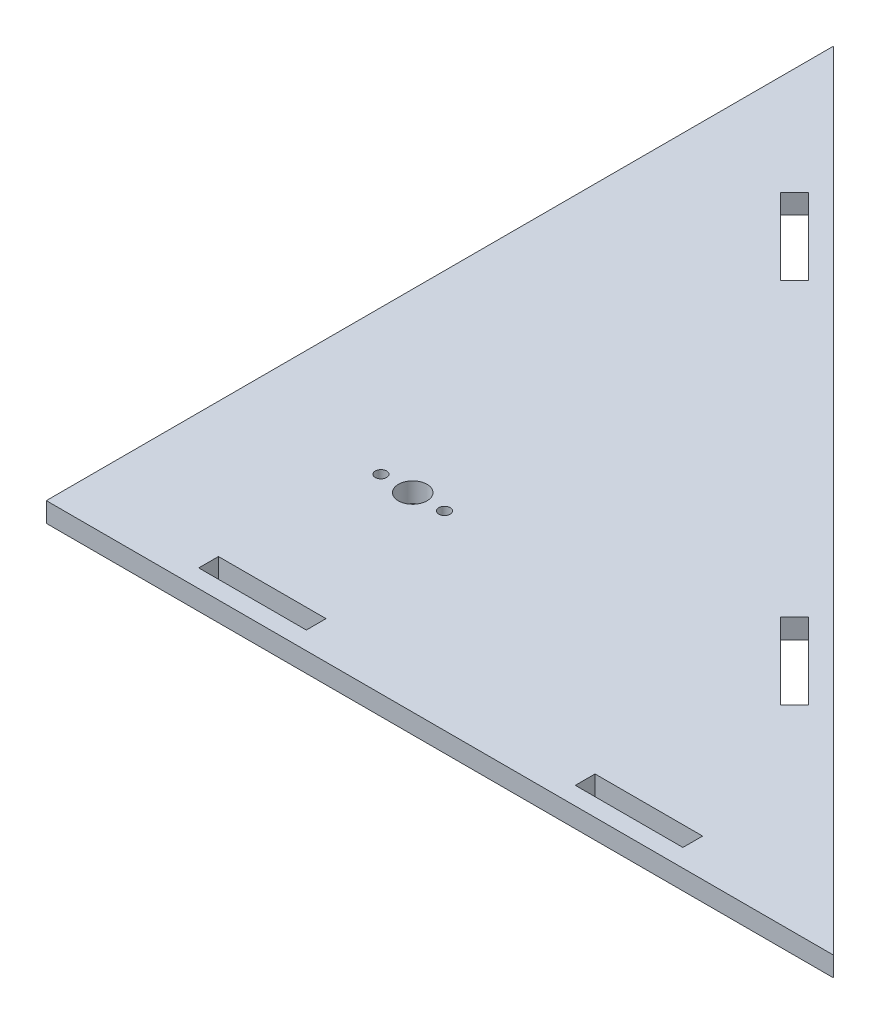
SolidWorks part; units mm, degrees
ref_plane "Front Plane" through (0, 0, 0) normal (0, 0, 1) x (1, 0, 0)
ref_plane "Top Plane" through (0, 0, 0) normal (0, 1, 0) x (1, 0, 0)
ref_plane "Right Plane" through (0, 0, 0) normal (1, 0, 0) x (0, 0, -1)
sketch "Sketch1" plane through (0, 0, 0) normal (0, 1, 0) x (1, 0, 0)
  line L0 (0, 0) -> (111.5314, 0)
  line L1 (111.5314, 0) -> (0, 111.5314)
  line L2 (0, 111.5314) -> (0, 0)
  line L3 (3.4521, 26.9374) -> (41.5139, 26.9374) construction
  line L4 (19.05, 5.334) -> (34.29, 5.334)
  line L5 (19.05, 5.334) -> (19.05, 2.54)
  line L6 (19.05, 2.54) -> (34.29, 2.54)
  line L7 (34.29, 5.334) -> (34.29, 2.54)
  line L8 (72.39, 5.334) -> (87.63, 5.334)
  line L9 (72.39, 5.334) -> (72.39, 2.54)
  line L10 (72.39, 2.54) -> (87.63, 2.54)
  line L11 (87.63, 5.334) -> (87.63, 2.54)
  line L12 (16.1645, 91.7748) -> (26.9408, 80.9985)
  line L13 (16.1645, 91.7748) -> (14.1888, 89.7992)
  line L14 (14.1888, 89.7992) -> (24.9651, 79.0229)
  line L15 (26.9408, 80.9985) -> (24.9651, 79.0229)
  line L16 (68.2499, 39.6894) -> (79.0263, 28.913)
  line L17 (68.2499, 39.6894) -> (66.2743, 37.7137)
  line L18 (66.2743, 37.7137) -> (77.0506, 26.9374)
  line L19 (79.0263, 28.913) -> (77.0506, 26.9374)
  circle A0 centre (24.9651, 26.9374) radius 2.032
  circle A1 centre (20.4642, 26.9374) radius 0.8065
  circle A2 centre (29.466, 26.9374) radius 0.8065
  dimension "D12" = 4.064
  dimension "D13" = 4.5009
  dimension "D15" = 1.6129
  dimension "D16" = 1.6129
  dimension "D1" = 111.5314
  dimension "D2" = 15.24
  dimension "D3" = 2.794
  dimension "D4" = 2.54
  dimension "D5" = 19.05
  dimension "D6" = 38.1
  dimension "D7" = 15.24
  dimension "D8" = 2.794
  dimension "D9" = 2.54
  dimension "D10" = 25.4
  dimension "D11" = 58.42
  dimension "D14" = 4.5009
extrude "Boss-Extrude1" add sketch "Sketch1" along normal blind 2.794
